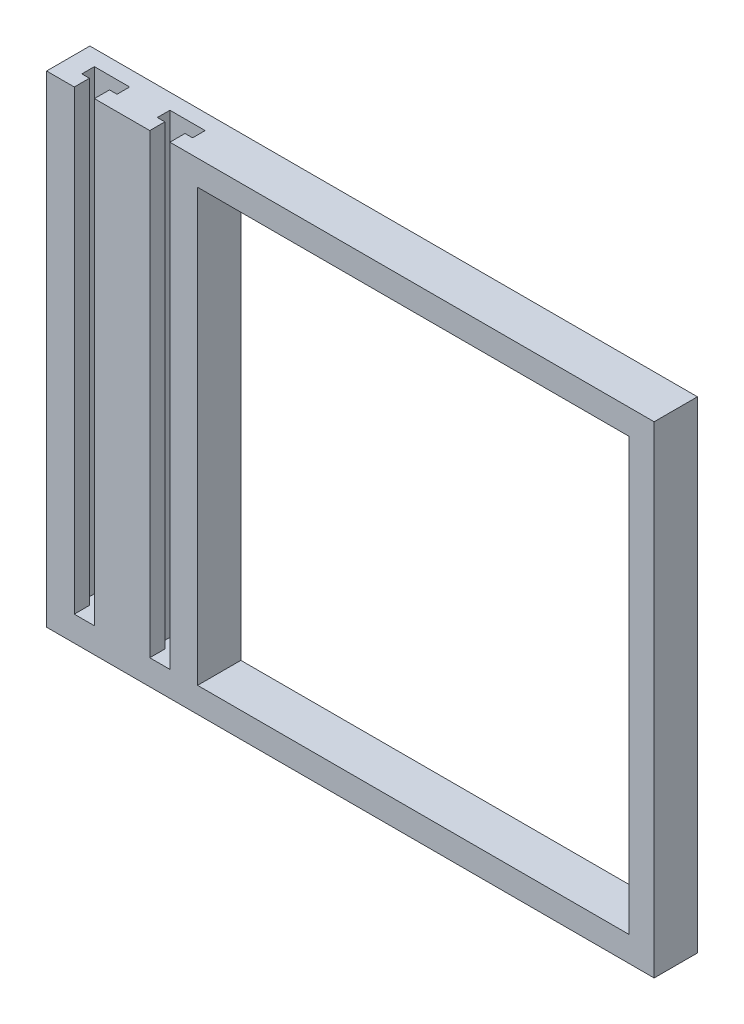
SolidWorks part; units mm, degrees
ref_plane "前视基准面" through (0, 0, 0) normal (0, 0, 1) x (1, 0, 0)
ref_plane "上视基准面" through (0, 0, 0) normal (0, 1, 0) x (1, 0, 0)
ref_plane "右视基准面" through (0, 0, 0) normal (1, 0, 0) x (0, 0, -1)
sketch "草图1" plane through (0, 0, 0) normal (0, 0, 1) x (1, 0, 0)
  line L0 (-47.85, 47.85) -> (47.85, 47.85)
  line L1 (47.85, -47.85) -> (47.85, 47.85)
  line L2 (-42.85, -42.85) -> (42.85, -42.85)
  line L3 (-42.85, -42.85) -> (-42.85, 42.85)
  line L4 (-42.85, 42.85) -> (42.85, 42.85)
  line L5 (42.85, -42.85) -> (42.85, 42.85)
  line L6 (-42.85, -42.85) -> (42.85, 42.85) construction
  line L7 (-42.85, 42.85) -> (42.85, -42.85) construction
  line L8 (-47.85, -47.85) -> (47.85, -47.85)
  line L9 (-47.85, -47.85) -> (-47.85, 47.85)
  point P1 (0, 0)
  dimension "D1" = 85.7
  dimension "D2" = 5
extrude "凸台-拉伸1" add sketch "草图1" along normal blind 8.6
sketch "草图2" plane through (-47.85, 0, 0) normal (-1, 0, 0) x (0, 0, 1)
  line L1 (0, 47.85) -> (8.6, 47.85)
  line L2 (0, 47.85) -> (0, -47.85)
  line L3 (0, -47.85) -> (8.6, -47.85)
  line L4 (8.6, 47.85) -> (8.6, -47.85)
  line L5 (4.3, -47.85) -> (4.3, 47.85) construction
  line L6 (0, 0) -> (8.6, 0) construction
  point P125 (4.3, 0)
extrude "凸台-拉伸2" add sketch "草图2" along normal blind 25
sketch "草图4" plane through (0, 0, 8.6) normal (0, 0, 1) x (1, 0, 0)
  line L0 (-42.85, 42.85) -> (-72.85, 42.85) construction
  line L1 (-72.85, -47.85) -> (-72.85, 47.85) construction
  line L2 (-57.85, 42.85) -> (-57.85, -47.85) construction
  line L3 (-72.85, -47.85) -> (47.85, -47.85) construction
  line L4 (-57.85, 42.85) -> (-72.85, -47.85) construction
  line L5 (-72.85, 42.85) -> (-57.85, -47.85) construction
  line L6 (-65.35, -2.5) -> (-65.35, 47.85) construction
  line L7 (47.85, 47.85) -> (-72.85, 47.85) construction
  line L8 (-65.35, 47.85) -> (-65.35, -42.85) construction
  line L9 (-66.85, 47.85) -> (-66.85, -42.85)
  line L10 (-63.85, 47.85) -> (-63.85, -42.85)
  line L11 (-66.85, 47.85) -> (-63.85, 47.85)
  line L12 (-66.85, -42.85) -> (-63.85, -42.85)
  dimension "D1" = 1.5
  dimension "D2" = 1.5
sketch "草图5" plane through (0, 47.85, 0) normal (0, 1, 0) x (1, 0, 0)
  line L0 (-72.85, 0) -> (-42.85, -8.6) construction
  line L1 (-67.35, -8.6) -> (-63.35, -8.6)
  line L2 (-42.85, 0) -> (-72.85, -8.6) construction
  line L3 (-57.85, -4.3) -> (-57.85, -8.6) construction
  line L4 (47.85, -8.6) -> (-72.85, -8.6) construction
  line L5 (-63.35, -8.6) -> (-63.35, -5.6)
  line L6 (-63.35, -5.6) -> (-61.85, -5.6)
  line L7 (-61.85, -5.6) -> (-61.85, -3.1)
  line L8 (-61.85, -3.1) -> (-68.85, -3.1)
  line L10 (-65.35, -3.1) -> (-65.35, -8.6) construction
  line L11 (-67.35, -5.6) -> (-68.85, -5.6)
  line L12 (-67.35, -8.6) -> (-67.35, -5.6)
  line L13 (-68.85, -5.6) -> (-68.85, -3.1)
  line L14 (-53.85, -5.6) -> (-53.85, -3.1)
  line L15 (-52.35, -5.6) -> (-53.85, -5.6)
  line L16 (-52.35, -8.6) -> (-52.35, -5.6)
  line L17 (-48.35, -8.6) -> (-52.35, -8.6)
  line L18 (-48.35, -8.6) -> (-48.35, -5.6)
  line L19 (-48.35, -5.6) -> (-46.85, -5.6)
  line L20 (-46.85, -5.6) -> (-46.85, -3.1)
  line L21 (-53.85, -3.1) -> (-46.85, -3.1)
  line L22 (-65.35, -8.6) -> (-50.35, -8.6) construction
  dimension "D1" = 2
  dimension "D2" = 3
  dimension "D3" = 1.5
  dimension "D4" = 2.5
  dimension "D5" = 15
extrude "切除-拉伸2" cut sketch "草图5" along direction (0, 1, 0) on the side against the normal up to surface (90.7 mm away)
